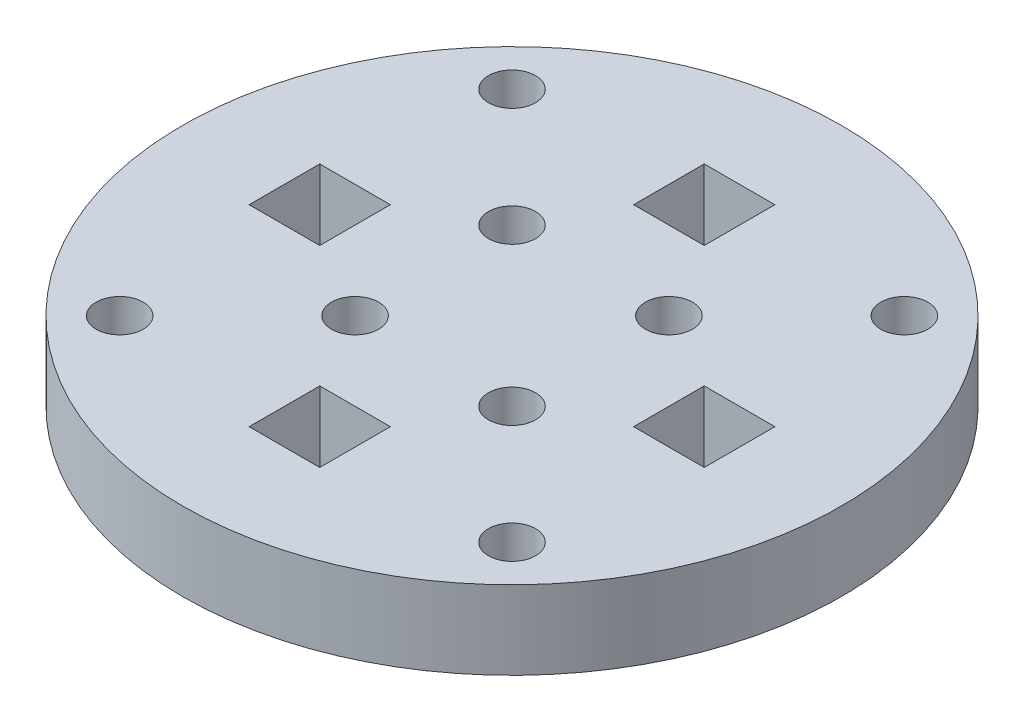
SolidWorks part; units mm, degrees
ref_plane "Front Plane" through (0, 0, 0) normal (0, 0, 1) x (1, 0, 0)
ref_plane "Top Plane" through (0, 0, 0) normal (0, 1, 0) x (1, 0, 0)
ref_plane "Right Plane" through (0, 0, 0) normal (1, 0, 0) x (0, 0, -1)
sketch "Sketch1" plane through (0, 0, 0) normal (0, 1, 0) x (1, 0, 0)
  line L0 (14.5, 2.25) -> (10, 2.25)
  line L5 (14.5, 2.25) -> (14.5, -2.25)
  line L6 (14.5, -2.25) -> (10, -2.25)
  line L7 (10, 2.25) -> (10, -2.25)
  line L12 (2.25, -14.5) -> (2.25, -10)
  line L13 (2.25, -14.5) -> (-2.25, -14.5)
  line L14 (-2.25, -14.5) -> (-2.25, -10)
  line L15 (2.25, -10) -> (-2.25, -10)
  line L17 (-2.25, 14.5) -> (2.25, 14.5)
  line L18 (-2.25, 14.5) -> (-2.25, 10)
  line L19 (-2.25, 10) -> (2.25, 10)
  line L20 (2.25, 14.5) -> (2.25, 10)
  line L24 (-14.5, -2.25) -> (-10, -2.25)
  line L25 (-14.5, -2.25) -> (-14.5, 2.25)
  line L26 (-14.5, 2.25) -> (-10, 2.25)
  line L27 (-10, -2.25) -> (-10, 2.25)
  circle A0 centre (0, 0) radius 21
  circle A1 centre (5, 5) radius 1.5
  circle A2 centre (-5, 5) radius 1.5
  circle A3 centre (5, -5) radius 1.5
  circle A4 centre (-5, -5) radius 1.5
  circle A5 centre (-12.5, 12.5) radius 1.5
  circle A6 centre (12.5, 12.5) radius 1.5
  circle A7 centre (12.5, -12.5) radius 1.5
  circle A8 centre (-12.5, -12.5) radius 1.5
  point P27 (0, 0)
  point P30 (0, 0.5)
  point P47 (0, 0)
  dimension "D6" = 3
  dimension "D10" = 42
  dimension "D11" = 4.5
  dimension "D4" = 3
  dimension "D5" = 3
  dimension "D7" = 3
  dimension "D8" = 3
  dimension "D16" = 4
  dimension "D2" = 5
  dimension "D3" = 5
  dimension "D9" = 4.5
  dimension "D12" = 2.25
  dimension "D13" = 10
  dimension "D14" = 12.5
  dimension "D15" = 12.5
extrude "Boss-Extrude1" add sketch "Sketch1" along normal mid plane 5
